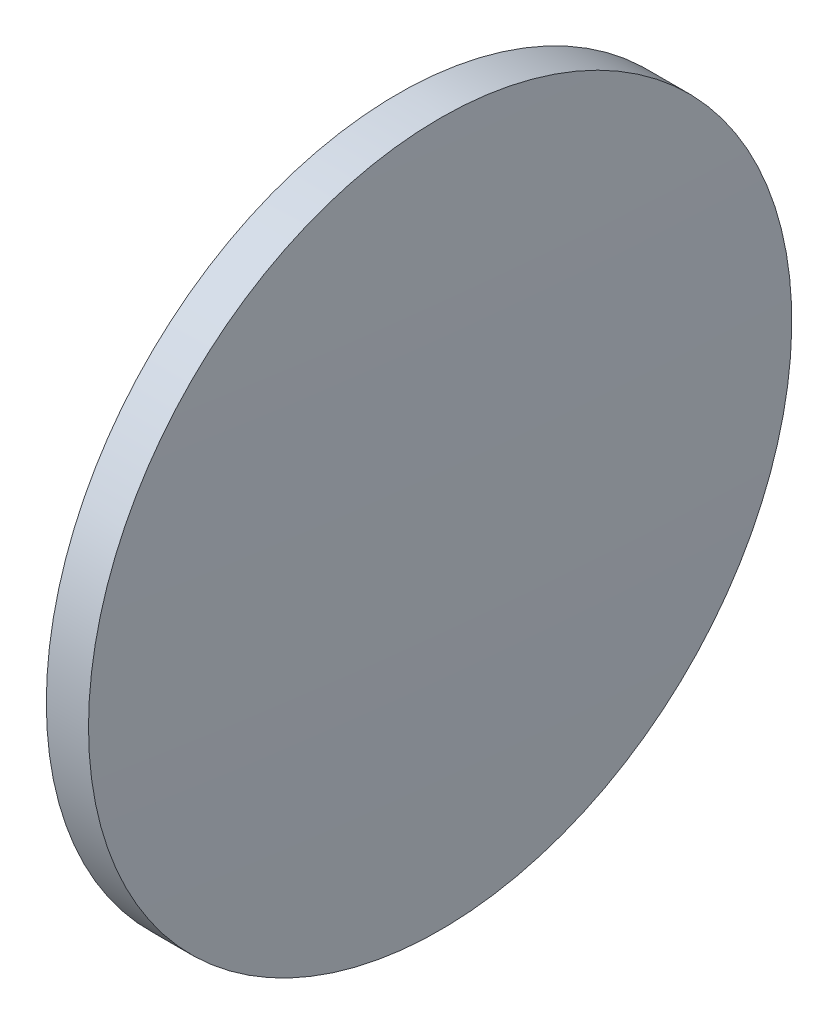
SolidWorks part; units mm, degrees
ref_plane "前视基准面" through (0, 0, 0) normal (0, 0, 1) x (1, 0, 0)
ref_plane "上视基准面" through (0, 0, 0) normal (0, 1, 0) x (1, 0, 0)
ref_plane "右视基准面" through (0, 0, 0) normal (1, 0, 0) x (0, 0, -1)
sketch "草图1" plane through (0, 0, 0) normal (0, 0, 1) x (1, 0, 0)
  line L0 (404.1524, 126.2827) -> (417.5981, 126.2827) construction
  line L1 (408.8944, 126.2827) -> (408.8944, 138.7827)
  line L2 (410.5944, 126.2827) -> (408.8944, 126.2827)
  line L5 (408.8944, 138.7827) -> (410.3944, 138.7827)
  arc A0 (410.5944, 126.2827) -> (410.3944, 138.7827) centre (19.8694, 126.2827) ccw
revolve "旋转1" add sketch "草图1" angle 360 about L0
